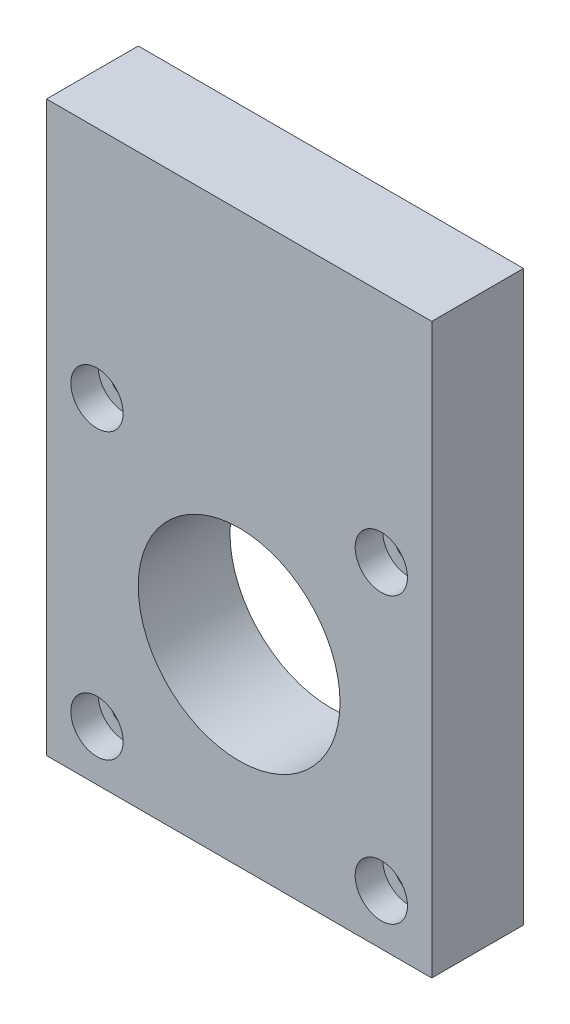
SolidWorks part; units mm, degrees
ref_plane "Front Plane" through (0, 0, 0) normal (0, 0, 1) x (1, 0, 0)
ref_plane "Top Plane" through (0, 0, 0) normal (0, 1, 0) x (1, 0, 0)
ref_plane "Right Plane" through (0, 0, 0) normal (1, 0, 0) x (0, 0, -1)
sketch "Sketch1" plane through (0, 0, 0) normal (0, 0, 1) x (1, 0, 0)
  line L1 (21, -31) -> (-21, -31)
  line L2 (21, -31) -> (21, 31)
  line L3 (21, 31) -> (-21, 31)
  line L4 (-21, -31) -> (-21, 31)
  point P4 (0, 31)
  point P5 (-21, 0)
  dimension "D1" = 42
  dimension "D2" = 62
extrude "Boss-Extrude1" add sketch "Sketch1" along normal blind 10
sketch "Sketch2" plane through (0, 0, 0) normal (0, 0, -1) x (-1, 0, 0)
  line L0 (-21, -31) -> (-21, 31) construction
  line L1 (21, -31) -> (-21, -31) construction
  line L2 (0, 14.7234) -> (0, -10) construction
  line L3 (0, -10) -> (-21, -10) construction
  circle A0 centre (15.5, 5.5) radius 1.5
  circle A1 centre (15.5, -25.5) radius 1.5
  circle A3 centre (-15.5, -25.5) radius 1.5
  circle A6 centre (-15.5, 5.5) radius 1.5
  circle A10 centre (0, -10) radius 11
  dimension "D6" = 36.5
  dimension "D7" = 3
  dimension "D8" = 22
  dimension "D3" = 5.5
  dimension "D5" = 21
extrude "Cut-Extrude1" cut sketch "Sketch2" against normal through all
sketch "Sketch3" plane through (0, 0, 10) normal (0, 0, 1) x (1, 0, 0)
  line L0 (0, 7.5) -> (0, -10) construction
  line L1 (0, -10) -> (-21, -10) construction
  line L2 (-21, 31) -> (-21, -31) construction
  circle A4 centre (-15.5, 5.5) radius 2.85
  circle A5 centre (15.5, 5.5) radius 2.85
  circle A6 centre (15.5, -25.5) radius 2.85
  circle A7 centre (-15.5, -25.5) radius 2.85
  dimension "D1" = 5.7
extrude "Cut-Extrude2" cut sketch "Sketch3" against normal blind 3
